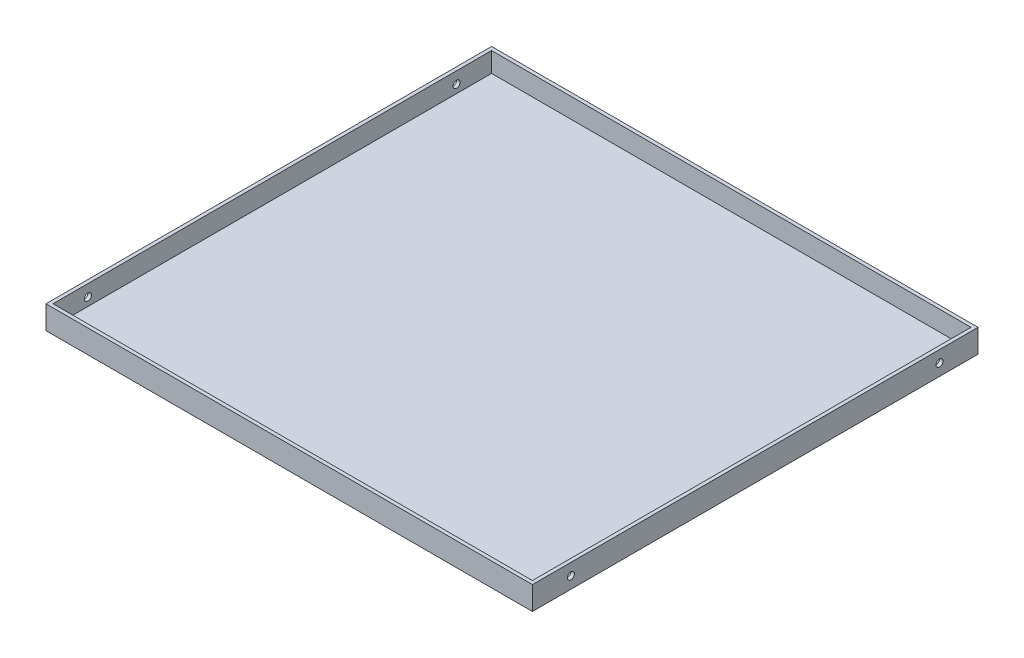
SolidWorks part; units mm, degrees
ref_plane "前基準面" through (0, 0, 0) normal (0, 0, 1) x (1, 0, 0)
ref_plane "上基準面" through (0, 0, 0) normal (0, 1, 0) x (1, 0, 0)
ref_plane "右基準面" through (0, 0, 0) normal (1, 0, 0) x (0, 0, -1)
sketch "草圖1" plane through (0, 0, 0) normal (0, 1, 0) x (1, 0, 0)
  line L0 (0, 0) -> (0, -382)
  line L1 (0, -382) -> (417, -382)
  line L2 (417, -382) -> (417, 0)
  line L3 (417, 0) -> (0, 0)
  dimension "D1" = 417
  dimension "D2" = 382
extrude "填料-伸長3" add sketch "草圖1" along normal blind 20
sketch "草圖2" plane through (0, 20, 0) normal (0, 1, 0) x (1, 0, 0)
  line L14 (3, -379) -> (414, -379)
  line L15 (414, -379) -> (414, -3)
  line L16 (414, -3) -> (3, -3)
  line L17 (3, -3) -> (3, -379)
  line L18 (3, -379) -> (414, -379)
  line L19 (414, -379) -> (414, -3)
  line L20 (414, -3) -> (3, -3)
  line L21 (3, -3) -> (3, -379)
  dimension "D1" = 3
extrude "除料-伸長1" cut sketch "草圖2" against normal blind 17 contours L18 L19 L20 L21
sketch "草圖3" plane through (417, 0, 0) normal (1, 0, 0) x (0, 0, -1)
  line L1 (0, 20) -> (0, 0) construction
  line L2 (-382, 20) -> (0, 20) construction
  line L3 (-382, 20) -> (-382, 0) construction
  circle A0 centre (-33, 10) radius 3
  circle A1 centre (-349, 10) radius 3
  dimension "D1" = 6
  dimension "D4" = 6
  dimension "D2" = 33
  dimension "D3" = 10
  dimension "D5" = 33
  dimension "D6" = 10
extrude "除料-伸長2" cut sketch "草圖3" against normal through all
